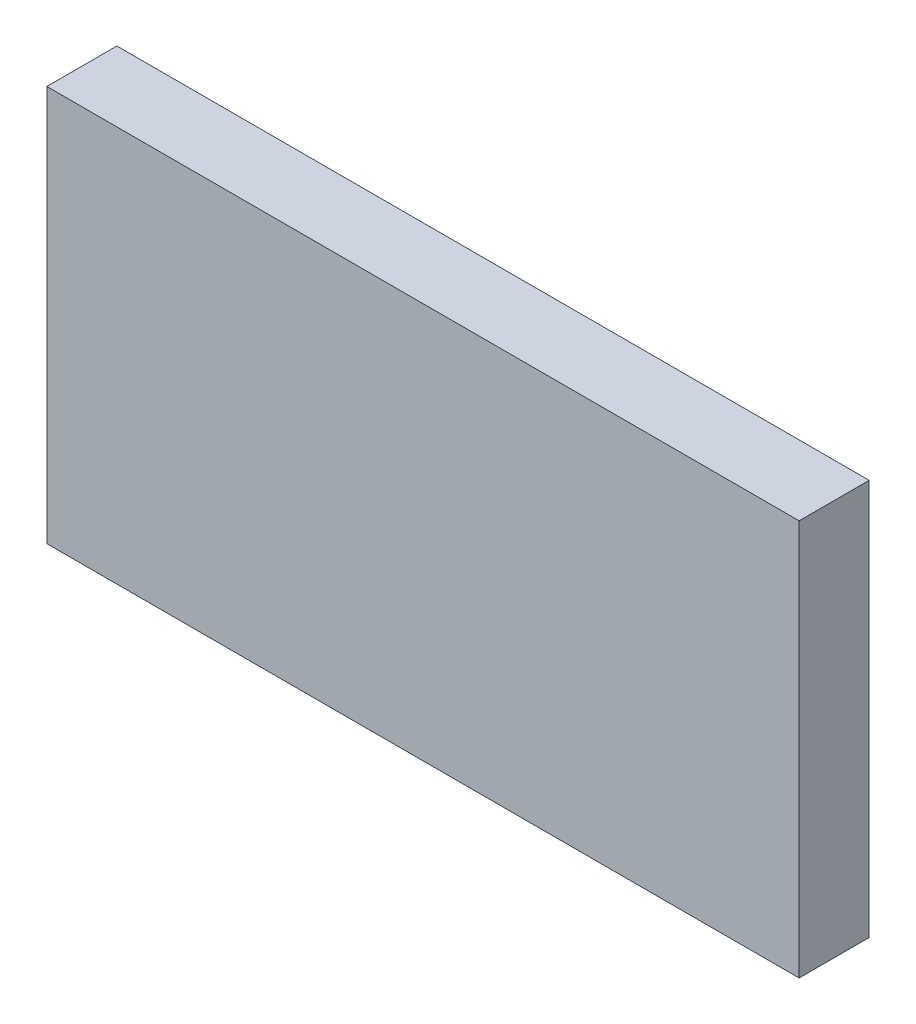
SolidWorks part; units mm, degrees
ref_plane "Plano frontal" through (0, 0, 0) normal (0, 0, 1) x (1, 0, 0)
ref_plane "Plano superior" through (0, 0, 0) normal (0, 1, 0) x (1, 0, 0)
ref_plane "Plano direito" through (0, 0, 0) normal (1, 0, 0) x (0, 0, -1)
sketch "Esboço1" plane through (0, 0, 0) normal (0, 0, 1) x (1, 0, 0)
  line L1 (-169.9099, -48.9937) -> (77.0901, -48.9937)
  line L2 (-169.9099, -48.9937) -> (-169.9099, 81.0063)
  line L3 (-169.9099, 81.0063) -> (77.0901, 81.0063)
  line L4 (77.0901, -48.9937) -> (77.0901, 81.0063)
  line L5 (-169.9099, -48.9937) -> (77.0901, 81.0063) construction
  line L6 (-169.9099, 81.0063) -> (77.0901, -48.9937) construction
  point P0 (-46.4099, 16.0063)
  dimension "D1" = 130
  dimension "D2" = 247
extrude "Ressalto-extrusão1" add sketch "Esboço1" along normal blind 23
